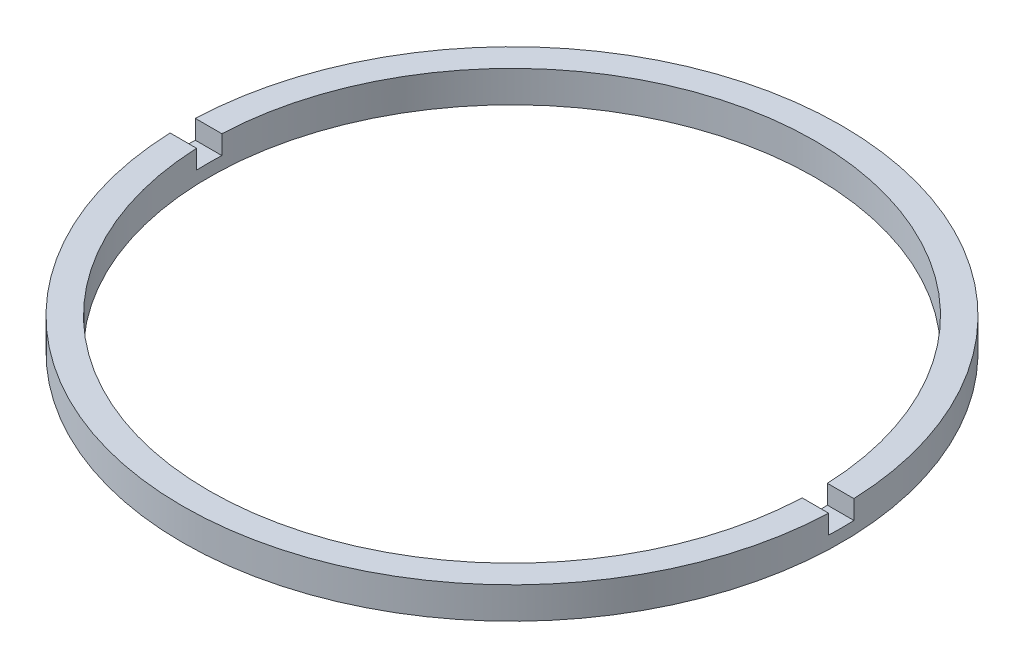
SolidWorks part; units mm, degrees
ref_plane "前视基准面" through (0, 0, 0) normal (0, 0, 1) x (1, 0, 0)
ref_plane "上视基准面" through (0, 0, 0) normal (0, 1, 0) x (1, 0, 0)
ref_plane "右视基准面" through (0, 0, 0) normal (1, 0, 0) x (0, 0, -1)
sketch "草图1" plane through (0, 0, 0) normal (0, 0, 1) x (1, 0, 0)
  line L0 (0, 56.2608) -> (0, -99.1922) construction
  line L1 (24, -1.9642) -> (26.1, -1.9642)
  line L4 (26.1, -1.9642) -> (26.1, -4.4642)
  line L5 (24, -4.4642) -> (24, -1.9642)
  line L7 (24, -4.4642) -> (26.1, -4.4642)
  dimension "D1" = 2.5
  dimension "D2" = 26.1
  dimension "D3" = 24
revolve "旋转1" add sketch "草图1" angle 360 about L0
cosmetic thread "装饰螺纹线1" parameters "D2"=52
sketch "草图2" plane through (0, -1.9642, 0) normal (0, 1, 0) x (1, 0, 0)
  line L0 (-28.67, 0) -> (29.9422, 0) construction
  line L2 (-26.8525, 1) -> (26.8525, 1)
  line L3 (-26.8525, 1) -> (-26.8525, -1)
  line L4 (-26.8525, -1) -> (26.8525, -1)
  line L5 (26.8525, 1) -> (26.8525, -1)
  line L6 (-26.8525, 1) -> (26.8525, -1) construction
  line L7 (-26.8525, -1) -> (26.8525, 1) construction
  point P3 (0, 0)
  dimension "D1" = 2
extrude "切除-拉伸1" cut sketch "草图2" against normal blind 1.5
